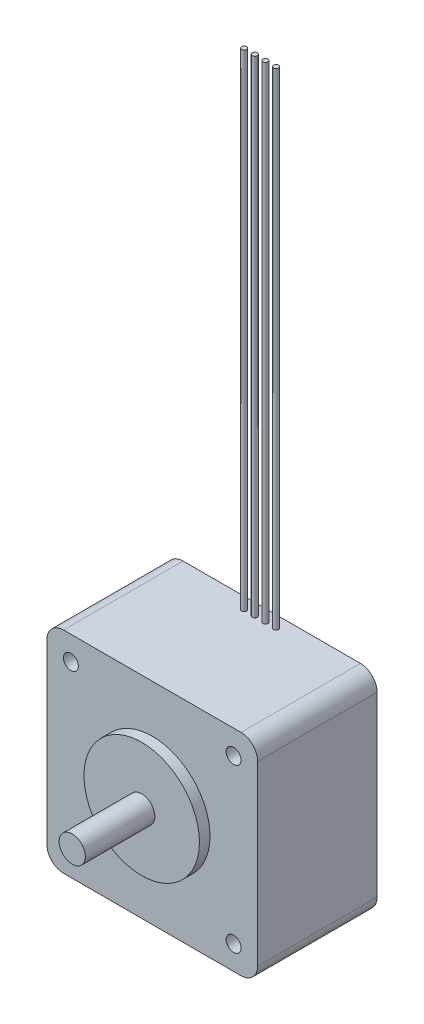
SolidWorks part; units mm, degrees
material "Plain Carbon Steel"
ref_plane "Front Plane" through (0, 0, 0) normal (0, 0, 1) x (1, 0, 0)
ref_plane "Top Plane" through (0, 0, 0) normal (0, 1, 0) x (1, 0, 0)
ref_plane "Right Plane" through (0, 0, 0) normal (1, 0, 0) x (0, 0, -1)
ref_plane "Plane1" through (0, 0, 22.7584) normal (0, 0, 1) x (1, 0, 0)
sketch "Sketch1" plane through (0, 0, 22.7584) normal (0, 0, 1) x (1, 0, 0)
  line L0 (20.066, -20.066) -> (20.066, 20.066)
  line L1 (20.066, 20.066) -> (-20.066, 20.066)
  line L2 (-20.066, 20.066) -> (-20.066, -20.066)
  line L3 (-20.066, -20.066) -> (20.066, -20.066)
extrude "Boss-Extrude1" add sketch "Sketch1" against normal blind 22.7584
ref_plane "Plane2" through (0, 0, 2.2098) normal (0, 0, -1) x (-1, 0, 0)
sketch "Sketch2" plane through (0, 0, 2.2098) normal (0, 0, -1) x (-1, 0, 0)
  line L0 (2.5654, 20.066) -> (3.048, 20.066)
  line L1 (3.048, 20.066) -> (3.048, 112.6856)
  line L2 (3.048, 112.6856) -> (2.5654, 112.6856)
  line L3 (2.5654, 112.6856) -> (2.5654, 20.066)
  line L4 (3.048, 20.066) -> (3.048, 112.6856) construction
revolve "Revolve1" add sketch "Sketch2" angle 360 about L4
sketch "Sketch3" plane through (0, 0, 2.2098) normal (0, 0, -1) x (-1, 0, 0)
  line L0 (-1.4986, 20.066) -> (-1.016, 20.066)
  line L1 (-1.016, 20.066) -> (-1.016, 112.6856)
  line L2 (-1.016, 112.6856) -> (-1.4986, 112.6856)
  line L3 (-1.4986, 112.6856) -> (-1.4986, 20.066)
  line L4 (-1.016, 20.066) -> (-1.016, 112.6856) construction
revolve "Revolve2" add sketch "Sketch3" angle 360 about L4
sketch "Sketch4" plane through (0, 0, 2.2098) normal (0, 0, -1) x (-1, 0, 0)
  line L0 (-3.5306, 20.066) -> (-3.048, 20.066)
  line L1 (-3.048, 20.066) -> (-3.048, 112.6856)
  line L2 (-3.048, 112.6856) -> (-3.5306, 112.6856)
  line L3 (-3.5306, 112.6856) -> (-3.5306, 20.066)
  line L4 (-3.048, 20.066) -> (-3.048, 112.6856) construction
revolve "Revolve3" add sketch "Sketch4" angle 360 about L4
sketch "Sketch5" plane through (0, 0, 2.2098) normal (0, 0, -1) x (-1, 0, 0)
  line L0 (0.5334, 20.066) -> (1.016, 20.066)
  line L1 (1.016, 20.066) -> (1.016, 112.6856)
  line L2 (1.016, 112.6856) -> (0.5334, 112.6856)
  line L3 (0.5334, 112.6856) -> (0.5334, 20.066)
  line L4 (1.016, 20.066) -> (1.016, 112.6856) construction
revolve "Revolve4" add sketch "Sketch5" angle 360 about L4
sketch "Sketch6" plane through (0, 0, 0) normal (0, 1, 0) x (1, 0, 0)
  line L0 (10.9982, -22.7584) -> (0, -22.7584)
  line L1 (0, -22.7584) -> (0, -37.9984)
  line L2 (0, -37.9984) -> (2.4994, -37.9984)
  line L3 (2.4994, -37.9984) -> (2.4994, -24.765)
  line L4 (2.4994, -24.765) -> (10.9982, -24.765)
  line L5 (10.9982, -24.765) -> (10.9982, -22.7584)
  line L6 (0, -22.7584) -> (0, -37.9984) construction
revolve "Revolve5" add sketch "Sketch6" angle 360 about L6
hole_wizard "Hole1" positions "Sketch8" profile "Sketch7" legacy
sketch "Sketch8" plane through (0, 0, 22.7584) normal (0, 0, 1) x (1, 0, 0)
  point P0 (-15.494, 15.494)
sketch "Sketch7" plane through (-15.494, 15.494, 22.7584) normal (1, 0, 0) x (0, -1, 0)
  line L0 (0, 0) -> (0, 21.9964)
  line L1 (0, 21.9964) -> (1.4224, 21.9964)
  line L2 (1.4224, 21.9964) -> (1.4224, 0)
  line L3 (1.4224, 0) -> (0, 0)
  line L4 (0, 110) -> (0, -10) construction
  dimension "Diameter" = 2.8448
  dimension "Depth" = 21.9964
hole_wizard "Hole2" positions "Sketch10" profile "Sketch9" legacy
sketch "Sketch10" plane through (0, 0, 22.7584) normal (0, 0, 1) x (1, 0, 0)
  point P0 (15.494, 15.494)
sketch "Sketch9" plane through (15.494, 15.494, 22.7584) normal (1, 0, 0) x (0, -1, 0)
  line L0 (0, 0) -> (0, 21.9964)
  line L1 (0, 21.9964) -> (1.4224, 21.9964)
  line L2 (1.4224, 21.9964) -> (1.4224, 0)
  line L3 (1.4224, 0) -> (0, 0)
  line L4 (0, 110) -> (0, -10) construction
  dimension "Diameter" = 2.8448
  dimension "Depth" = 21.9964
hole_wizard "Hole3" positions "Sketch12" profile "Sketch11" legacy
sketch "Sketch12" plane through (0, 0, 22.7584) normal (0, 0, 1) x (1, 0, 0)
  point P0 (-15.494, -15.494)
sketch "Sketch11" plane through (-15.494, -15.494, 22.7584) normal (1, 0, 0) x (0, -1, 0)
  line L0 (0, 0) -> (0, 21.9964)
  line L1 (0, 21.9964) -> (1.4224, 21.9964)
  line L2 (1.4224, 21.9964) -> (1.4224, 0)
  line L3 (1.4224, 0) -> (0, 0)
  line L4 (0, 110) -> (0, -10) construction
  dimension "Diameter" = 2.8448
  dimension "Depth" = 21.9964
hole_wizard "Hole4" positions "Sketch14" profile "Sketch13" legacy
sketch "Sketch14" plane through (0, 0, 22.7584) normal (0, 0, 1) x (1, 0, 0)
  point P0 (15.494, -15.494)
sketch "Sketch13" plane through (15.494, -15.494, 22.7584) normal (1, 0, 0) x (0, -1, 0)
  line L0 (0, 0) -> (0, 21.9964)
  line L1 (0, 21.9964) -> (1.4224, 21.9964)
  line L2 (1.4224, 21.9964) -> (1.4224, 0)
  line L3 (1.4224, 0) -> (0, 0)
  line L4 (0, 110) -> (0, -10) construction
  dimension "Diameter" = 2.8448
  dimension "Depth" = 21.9964
fillet "Fillet1" radius 3.175 1 edges at (20.066, -20.066, 11.3792)
fillet "Fillet2" radius 3.175 1 edges at (-20.066, -20.066, 11.3792)
fillet "Fillet3" radius 3.175 1 edges at (20.066, 20.066, 11.3792)
fillet "Fillet4" radius 3.175 1 edges at (-20.066, 20.066, 11.3792)
